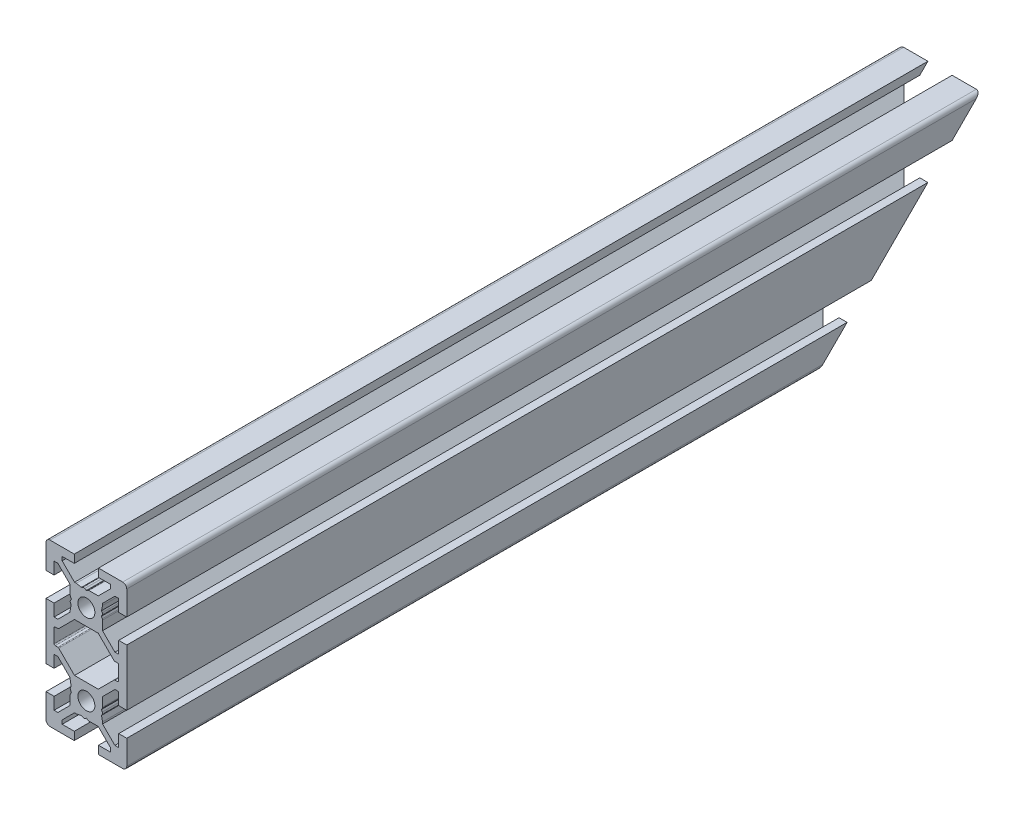
SolidWorks part; units mm, degrees
ref_plane "Front Plane" through (0, 0, 0) normal (0, 0, 1) x (1, 0, 0)
ref_plane "Top Plane" through (0, 0, 0) normal (0, 1, 0) x (1, 0, 0)
ref_plane "Right Plane" through (0, 0, 0) normal (1, 0, 0) x (0, 0, -1)
ref_plane "Plane1" through (0, 0, -600) normal (0, 0, -1) x (-1, 0, 0)
sketch "Sketch1" plane through (0, 0, -600) normal (0, 0, -1) x (-1, 0, 0)
  line L0 (8, 1.7) -> (8, -1.7)
  line L1 (7.7, -2) -> (7.0636, -2)
  line L2 (6.8515, -2.0879) -> (2.9393, -6)
  line L3 (2.9393, -6) -> (-2.9393, -6)
  line L4 (-2.9393, -6) -> (-6.8515, -2.0879)
  line L5 (-7.0636, -2) -> (-7.7, -2)
  line L6 (-8, -1.7) -> (-8, 1.7)
  line L7 (-7.7, 2) -> (-7.0636, 2)
  line L8 (-6.8515, 2.0879) -> (-2.9393, 6)
  line L9 (-2.9393, 6) -> (2.9393, 6)
  line L10 (2.9393, 6) -> (6.8515, 2.0879)
  line L11 (7.0636, 2) -> (7.7, 2)
  line L12 (10, -7) -> (10, 7)
  line L13 (10, 7) -> (8, 7)
  line L14 (8, 7) -> (8, 4)
  line L15 (8, 4) -> (7.0607, 4)
  line L16 (7.0607, 4) -> (4, 7.0607)
  line L17 (4, 7.0607) -> (4, 7.5)
  line L18 (4, 7.5) -> (3.751, 8.7811)
  line L19 (3.751, 8.7811) -> (3.933, 9.0964)
  line L20 (3.933, 9.5964) -> (3.7, 10)
  line L21 (3.7, 10) -> (3.933, 10.4036)
  line L22 (4, 10.6536) -> (4, 12.9393)
  line L23 (4, 12.9393) -> (7.0607, 16)
  line L24 (7.0607, 16) -> (8, 16)
  line L25 (8, 16) -> (8, 13)
  line L26 (8, 13) -> (10, 13)
  line L27 (10, 13) -> (10, 19)
  line L28 (9, 20) -> (3, 20)
  line L29 (3, 20) -> (3, 18)
  line L30 (3, 18) -> (6, 18)
  line L31 (6, 18) -> (6, 17.0607)
  line L32 (6, 17.0607) -> (2.9393, 14)
  line L33 (2.9393, 14) -> (2.5, 14)
  line L34 (2.5, 14) -> (1.2189, 13.751)
  line L35 (1.2189, 13.751) -> (0.9036, 13.933)
  line L36 (0.4036, 13.933) -> (0, 13.7)
  line L37 (0, 13.7) -> (-0.4036, 13.933)
  line L38 (-0.6536, 14) -> (-2.9393, 14)
  line L39 (-2.9393, 14) -> (-6, 17.0607)
  line L40 (-6, 17.0607) -> (-6, 18)
  line L41 (-6, 18) -> (-3, 18)
  line L42 (-3, 18) -> (-3, 20)
  line L43 (-3, 20) -> (-9, 20)
  line L44 (-10, 19) -> (-10, 13)
  line L45 (-10, 13) -> (-8, 13)
  line L46 (-8, 13) -> (-8, 16)
  line L47 (-8, 16) -> (-7.0607, 16)
  line L48 (-7.0607, 16) -> (-4, 12.9393)
  line L49 (-4, 12.9393) -> (-4, 12.5)
  line L50 (-4, 12.5) -> (-3.751, 11.2189)
  line L51 (-3.751, 11.2189) -> (-3.933, 10.9036)
  line L52 (-3.933, 10.4036) -> (-3.7, 10)
  line L53 (-3.7, 10) -> (-3.933, 9.5964)
  line L54 (-4, 9.3464) -> (-4, 7.0607)
  line L55 (-4, 7.0607) -> (-7.0607, 4)
  line L56 (-7.0607, 4) -> (-8, 4)
  line L57 (-8, 4) -> (-8, 7)
  line L58 (-8, 7) -> (-10, 7)
  line L59 (-10, 7) -> (-10, -7)
  line L60 (-10, -7) -> (-8, -7)
  line L61 (-8, -7) -> (-8, -4)
  line L62 (-8, -4) -> (-7.0607, -4)
  line L63 (-7.0607, -4) -> (-4, -7.0607)
  line L64 (-4, -7.0607) -> (-4, -9.3464)
  line L65 (-3.933, -9.5964) -> (-3.7, -10)
  line L66 (-3.7, -10) -> (-3.933, -10.4036)
  line L67 (-3.933, -10.9036) -> (-3.751, -11.2189)
  line L68 (-3.751, -11.2189) -> (-4, -12.5)
  line L69 (-4, -12.5) -> (-4, -12.9393)
  line L70 (-4, -12.9393) -> (-7.0607, -16)
  line L71 (-7.0607, -16) -> (-8, -16)
  line L72 (-8, -16) -> (-8, -13)
  line L73 (-8, -13) -> (-10, -13)
  line L74 (-10, -13) -> (-10, -19)
  line L75 (-9, -20) -> (-3, -20)
  line L76 (-3, -20) -> (-3, -18)
  line L77 (-3, -18) -> (-6, -18)
  line L78 (-6, -18) -> (-6, -17.0607)
  line L79 (-6, -17.0607) -> (-2.9393, -14)
  line L80 (-2.9393, -14) -> (-0.6536, -14)
  line L81 (-0.4036, -13.933) -> (0, -13.7)
  line L82 (0, -13.7) -> (0.4036, -13.933)
  line L83 (0.9036, -13.933) -> (1.2189, -13.751)
  line L84 (1.2189, -13.751) -> (2.5, -14)
  line L85 (2.5, -14) -> (2.9393, -14)
  line L86 (2.9393, -14) -> (6, -17.0607)
  line L87 (6, -17.0607) -> (6, -18)
  line L88 (6, -18) -> (3, -18)
  line L89 (3, -18) -> (3, -20)
  line L90 (3, -20) -> (9, -20)
  line L91 (10, -19) -> (10, -13)
  line L92 (10, -13) -> (8, -13)
  line L93 (8, -13) -> (8, -16)
  line L94 (8, -16) -> (7.0607, -16)
  line L95 (7.0607, -16) -> (4, -12.9393)
  line L96 (4, -12.9393) -> (4, -10.6536)
  line L97 (3.933, -10.4036) -> (3.7, -10)
  line L98 (3.7, -10) -> (3.933, -9.5964)
  line L99 (3.933, -9.0964) -> (3.751, -8.7811)
  line L100 (3.751, -8.7811) -> (4, -7.5)
  line L101 (4, -7.5) -> (4, -7.0607)
  line L102 (4, -7.0607) -> (7.0607, -4)
  line L103 (7.0607, -4) -> (8, -4)
  line L104 (8, -4) -> (8, -7)
  line L105 (8, -7) -> (10, -7)
  circle A0 centre (0, -10) radius 2.1
  circle A1 centre (0, 10) radius 2.1
  arc A2 (7.7, 2) -> (8, 1.7) centre (7.7, 1.7) cw
  arc A3 (8, -1.7) -> (7.7, -2) centre (7.7, -1.7) cw
  arc A4 (7.0636, -2) -> (6.8515, -2.0879) centre (7.0636, -2.3) ccw
  arc A5 (-6.8515, -2.0879) -> (-7.0636, -2) centre (-7.0636, -2.3) ccw
  arc A6 (-7.7, -2) -> (-8, -1.7) centre (-7.7, -1.7) cw
  arc A7 (-8, 1.7) -> (-7.7, 2) centre (-7.7, 1.7) cw
  arc A8 (-7.0636, 2) -> (-6.8515, 2.0879) centre (-7.0636, 2.3) ccw
  arc A9 (6.8515, 2.0879) -> (7.0636, 2) centre (7.0636, 2.3) ccw
  arc A10 (3.933, 9.0964) -> (3.933, 9.5964) centre (3.5, 9.3464) ccw
  arc A11 (3.933, 10.4036) -> (4, 10.6536) centre (3.5, 10.6536) ccw
  arc A12 (10, 19) -> (9, 20) centre (9, 19) ccw
  arc A13 (0.9036, 13.933) -> (0.4036, 13.933) centre (0.6536, 13.5) ccw
  arc A14 (-0.4036, 13.933) -> (-0.6536, 14) centre (-0.6536, 13.5) ccw
  arc A15 (-9, 20) -> (-10, 19) centre (-9, 19) ccw
  arc A16 (-3.933, 10.9036) -> (-3.933, 10.4036) centre (-3.5, 10.6536) ccw
  arc A17 (-3.933, 9.5964) -> (-4, 9.3464) centre (-3.5, 9.3464) ccw
  arc A18 (-4, -9.3464) -> (-3.933, -9.5964) centre (-3.5, -9.3464) ccw
  arc A19 (-3.933, -10.4036) -> (-3.933, -10.9036) centre (-3.5, -10.6536) ccw
  arc A20 (-10, -19) -> (-9, -20) centre (-9, -19) ccw
  arc A21 (-0.6536, -14) -> (-0.4036, -13.933) centre (-0.6536, -13.5) ccw
  arc A22 (0.4036, -13.933) -> (0.9036, -13.933) centre (0.6536, -13.5) ccw
  arc A23 (9, -20) -> (10, -19) centre (9, -19) ccw
  arc A24 (4, -10.6536) -> (3.933, -10.4036) centre (3.5, -10.6536) ccw
  arc A25 (3.933, -9.5964) -> (3.933, -9.0964) centre (3.5, -9.3464) ccw
  dimension "D1" = 4.2
  dimension "D3" = 0.3
  dimension "D4" = 0.3
  dimension "D5" = 0.3
  dimension "D6" = 0.3
  dimension "D7" = 0.3
  dimension "D8" = 0.3
  dimension "D9" = 0.3
  dimension "D10" = 0.5
  dimension "D11" = 0.5
  dimension "D12" = 1
  dimension "D13" = 0.5
  dimension "D14" = 0.5
  dimension "D15" = 1
  dimension "D16" = 0.5
  dimension "D17" = 0.5
  dimension "D18" = 0.5
  dimension "D19" = 0.5
  dimension "D20" = 0.4036
  dimension "D21" = 0.5
  dimension "D22" = 0.5
  dimension "D23" = 1
  dimension "D24" = 0.5
  dimension "D25" = 0.5
  dimension "D26" = 0.4036
  dimension "D27" = 0.6536
  dimension "D28" = 0.6536
  dimension "D29" = 0.9036
  dimension "D30" = 0.9036
  dimension "D31" = 1.2189
  dimension "D32" = 1.2189
  dimension "D33" = 2.5
  dimension "D34" = 2.5
  dimension "D35" = 2.9393
  dimension "D36" = 2.9393
  dimension "D37" = 3
  dimension "D38" = 3.5
  dimension "D39" = 6
  dimension "D40" = 6.8515
  dimension "D41" = 3.7
  dimension "D42" = 3.7
  dimension "D43" = 3.751
  dimension "D44" = 3.751
  dimension "D45" = 3.933
  dimension "D46" = 3.933
  dimension "D47" = 6.8515
  dimension "D48" = 7.0607
  dimension "D49" = 7.0607
  dimension "D50" = 7.0636
  dimension "D51" = 7.0636
  dimension "D52" = 8
  dimension "D53" = 10
  dimension "D54" = 3
  dimension "D55" = 4
  dimension "D56" = 6
  dimension "D57" = 6.8515
  dimension "D58" = 6.8515
  dimension "D59" = 7.0607
  dimension "D60" = 7.0607
  dimension "D61" = 0.4036
  dimension "D62" = 0.4036
  dimension "D63" = 0.6536
  dimension "D64" = 0.6536
  dimension "D65" = 2.9393
  dimension "D66" = 2.9393
  dimension "D67" = 8
  dimension "D68" = 2
  dimension "D69" = 3.5
  dimension "D70" = 3.5
  dimension "D71" = 3.7
  dimension "D72" = 3.7
  dimension "D73" = 3.751
  dimension "D74" = 3.751
  dimension "D75" = 3.933
  dimension "D76" = 3.933
  dimension "D77" = 4
  dimension "D78" = 6
  dimension "D79" = 7
  dimension "D80" = 7.0607
  dimension "D81" = 7.0607
  dimension "D82" = 7.5
  dimension "D83" = 8.7811
  dimension "D84" = 9.0964
  dimension "D85" = 9.3464
  dimension "D86" = 9.3464
  dimension "D87" = 9.5964
  dimension "D88" = 9.5964
  dimension "D89" = 10.4036
  dimension "D90" = 12.5
  dimension "D91" = 13
  dimension "D92" = 13.5
  dimension "D93" = 13.5
  dimension "D94" = 18
  dimension "D95" = 20
  dimension "D96" = 2
  dimension "D97" = 4
  dimension "D98" = 6
  dimension "D99" = 7
  dimension "D100" = 7.0607
  dimension "D101" = 7.0607
  dimension "D102" = 7.5
  dimension "D103" = 8.7811
  dimension "D104" = 9.0964
  dimension "D105" = 9.3464
  dimension "D106" = 9.3464
  dimension "D107" = 9.5964
  dimension "D108" = 9.5964
  dimension "D109" = 10.4036
  dimension "D110" = 12.5
  dimension "D111" = 13
  dimension "D112" = 18
extrude "Boss-Extrude1" add sketch "Sketch1" against normal blind 211.39
sketch "Sketch2" plane through (-10, 0, 0) normal (-1, 0, 0) x (0, 0, 1)
  line L0 (-600, 20) -> (-560, -20)
  line L1 (-388.61, -20) -> (-600, -20) construction
  line L2 (-560, -20) -> (-600, -20)
  line L3 (-600, -20) -> (-600, 20)
  dimension "D1" = 45
extrude "Cut-Extrude1" cut sketch "Sketch2" against normal through all
